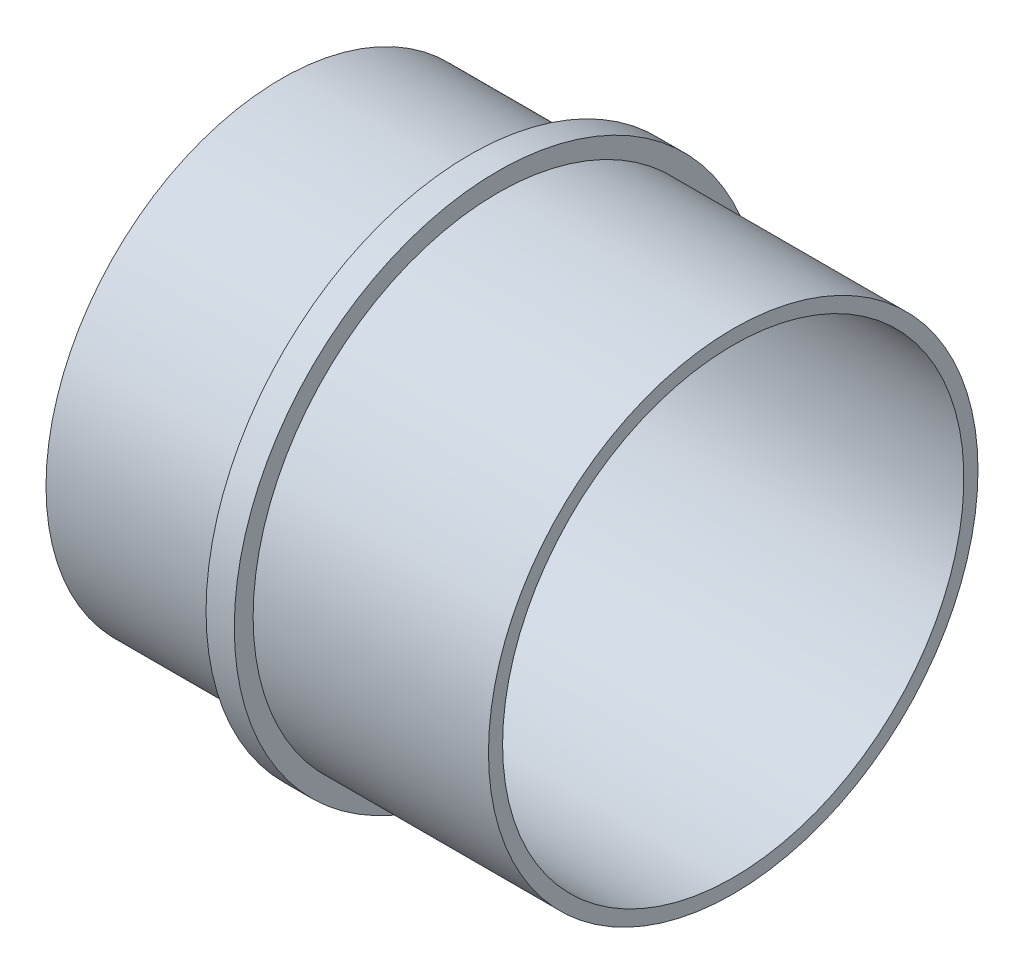
SolidWorks part; units mm, degrees
ref_plane "Plan de face" through (0, 0, 0) normal (0, 0, 1) x (1, 0, 0)
ref_plane "Plan de dessus" through (0, 0, 0) normal (0, 1, 0) x (1, 0, 0)
ref_plane "Plan de droite" through (0, 0, 0) normal (1, 0, 0) x (0, 0, -1)
sketch "Esquisse1" plane through (0, 0, 0) normal (0, 0, 1) x (1, 0, 0)
  line L0 (0, 0) -> (24, 0)
  line L1 (24, 0) -> (24, 0.75)
  line L2 (24, 0.75) -> (11.5, 0.75)
  line L3 (11.5, 0.75) -> (11.5, 1.75)
  line L4 (11.5, 1.75) -> (10, 1.75)
  line L5 (10, 1.75) -> (10, 0.25)
  line L6 (10, 0.25) -> (0, 0.25)
  line L7 (0, 0.25) -> (0, 0)
  line L8 (-3, -12.25) -> (27, -12.25) construction
  dimension "D1" = 10
  dimension "D2" = 1.5
  dimension "D3" = 24
  dimension "D4" = 12.25
  dimension "D5" = 12.5
  dimension "D6" = 14
  dimension "D7" = 13
revolve "Révolution1" add sketch "Esquisse1" angle 360 about L8
